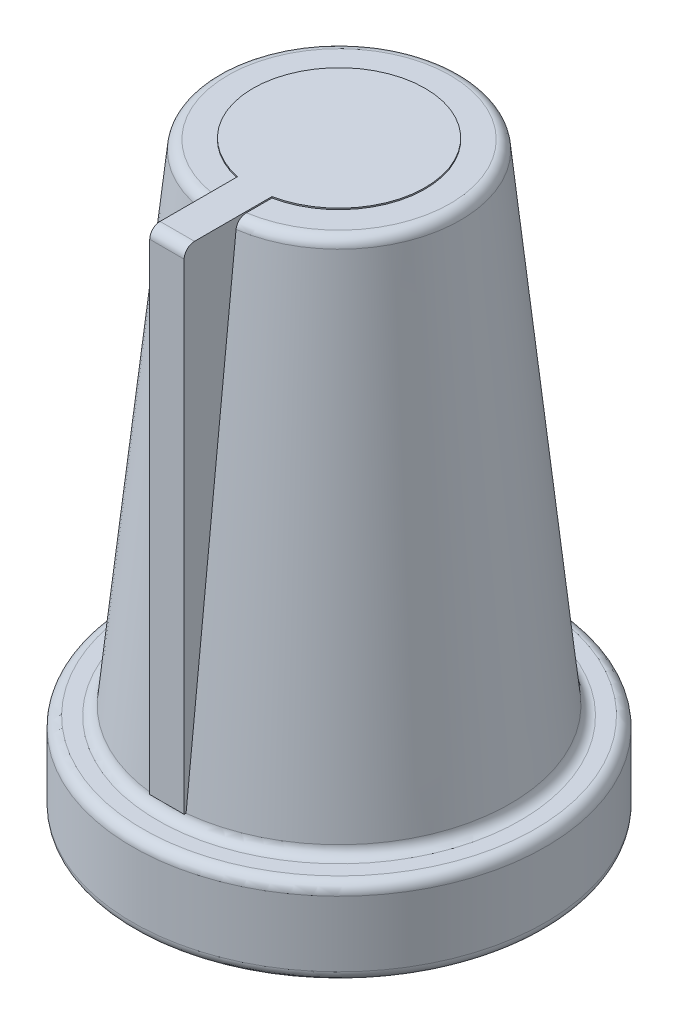
SolidWorks part; units mm, degrees
ref_plane "Alzado" through (0, 0, 0) normal (0, 0, 1) x (1, 0, 0)
ref_plane "Planta" through (0, 0, 0) normal (0, 1, 0) x (1, 0, 0)
ref_plane "Vista lateral" through (0, 0, 0) normal (1, 0, 0) x (0, 0, -1)
sketch "Croquis1" plane through (0, 0, 0) normal (0, 0, 1) x (1, 0, 0)
  line L0 (-2.5, 9.4375) -> (0, 9.4375)
  line L1 (-2.5, -7) -> (3.5, -7) construction
  line L2 (-2.5, -7) -> (-2.5, 10) construction
  line L3 (-2.5, 10) -> (3.5, 10) construction
  line L4 (3.5, -7) -> (3.5, 10) construction
  line L5 (0, 9.4375) -> (0, 10)
  line L6 (0, 10) -> (0.7294, 10)
  line L7 (-2.5, -4.5) -> (3.5, -4.5) construction
  line L8 (1.0278, 9.7308) -> (2.4699, -4.2308)
  line L9 (2.7683, -4.5) -> (3.2, -4.5)
  line L10 (3.5, -4.8) -> (3.5, -6.7)
  line L11 (3.2, -7) -> (3, -7)
  line L12 (3, -7) -> (3, -5.3)
  line L13 (2.7, -5) -> (0.5, -5)
  line L14 (0.5, -5) -> (0.5, 8.6375)
  line L15 (0.2, 8.9375) -> (-2.5, 8.9375)
  line L16 (-2.5, 9.4375) -> (-2.5, 8.9375)
  line L17 (-2.5, 9.4375) -> (-2.5, 8.9375)
  arc A0 (3, -5.3) -> (2.7, -5) centre (2.7, -5.3) ccw
  arc A1 (3.5, -6.7) -> (3.2, -7) centre (3.2, -6.7) cw
  arc A2 (3.2, -4.5) -> (3.5, -4.8) centre (3.2, -4.8) cw
  arc A3 (2.4699, -4.2308) -> (2.7683, -4.5) centre (2.7683, -4.2) ccw
  arc A4 (0.5, 8.6375) -> (0.2, 8.9375) centre (0.2, 8.6375) ccw
  arc A5 (0.7294, 10) -> (1.0278, 9.7308) centre (0.7294, 9.7) cw
  point P0 (0, 0)
  point P28 (2.4977, -4.5)
  point P31 (0.5, 8.9375)
  point P34 (1, 10)
  dimension "D10" = 0.3
  dimension "D1" = 6
  dimension "D2" = 17
  dimension "D3" = 3.5
  dimension "D4" = 2.5
  dimension "D5" = 2.5
  dimension "D6" = 0.5
  dimension "D7" = 0.5
  dimension "D8" = 3
  dimension "D9" = 0.5
revolve "Revolución1" add sketch "Croquis1" angle 360 about L2
sketch "Croquis2" plane through (0, 0, 0) normal (0, 0, 1) x (1, 0, 0)
  line L0 (-2.5, -4.2308) -> (-2.5, 10) construction
  line L1 (2.4699, -4.2308) -> (-7.4699, -4.2308) construction
  line L2 (0, 10) -> (-5, 10) construction
  line L4 (-3, -4.2308) -> (-2, -4.2308)
  line L5 (-3, -4.2308) -> (-3, 10)
  line L6 (-3, 10) -> (-2, 10)
  line L7 (-2, -4.2308) -> (-2, 10)
  line L8 (-3, -4.2308) -> (-2, 10) construction
  line L9 (-3, 10) -> (-2, -4.2308) construction
  point P6 (-2.5, 2.8846)
  dimension "D1" = 1
extrude "Saliente-Extruir1" add sketch "Croquis2" along normal blind 5
sketch "Croquis3" plane through (0, 9.4375, 0) normal (0, 1, 0) x (1, 0, 0)
  line L0 (-3, 0) -> (-2, 0) construction
  line L1 (-3, -4.9447) -> (-2, -5)
  line L2 (-2, -5) -> (-2, -2.4495)
  line L3 (-3, -4.9447) -> (-3, -2.4495)
  arc A0 (-2, -2.4495) -> (-3, -2.4495) centre (-2.5, 0) ccw
extrude "Saliente-Extruir3" add sketch "Croquis3" along normal blind 0.6
sketch "Croquis4" plane through (-2, 0, 0) normal (1, 0, 0) x (0, 0, -1)
  line L5 (-5, 9.7375) -> (-5, 10.0375)
  line L6 (-5, 10.0375) -> (-4.7, 10.0375)
  arc A0 (-5, 9.7375) -> (-4.7, 10.0375) centre (-4.7, 9.7375) cw
  point P11 (-5, 10.0375)
  dimension "D1" = 0.3
extrude "Cortar-Extruir1" cut sketch "Croquis4" against normal blind 10.6
sketch "Croquis5" plane through (0, -5, 0) normal (0, -1, 0) x (1, 0, 0)
  line L0 (-2, 0) -> (-3, 0) construction
  circle A0 centre (-2.5, 0) radius 3
extrude "Cortar-Extruir2" cut sketch "Croquis5" against normal up to surface (13.9375 mm away) up to face at (-2.5, 8.9375, -0.0117)
